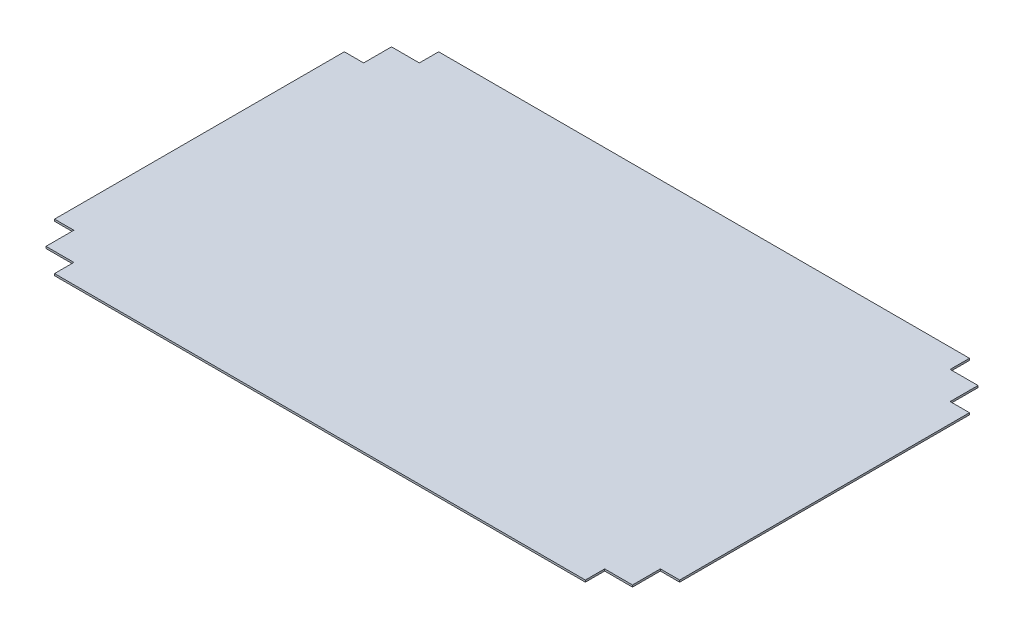
SolidWorks part; units mm, degrees
ref_plane "Front Plane" through (0, 0, 0) normal (0, 0, 1) x (1, 0, 0)
ref_plane "Top Plane" through (0, 0, 0) normal (0, 1, 0) x (1, 0, 0)
ref_plane "Right Plane" through (0, 0, 0) normal (1, 0, 0) x (0, 0, -1)
sketch "Sketch1" plane through (0, 0, 0) normal (0, 1, 0) x (1, 0, 0)
  line L0 (-325.4993, 150.9011) -> (-307.0007, 150.9011)
  line L1 (-307.0007, 150.9011) -> (-305.4007, 150.9011)
  line L2 (-305.4007, 150.9011) -> (-305.4007, 179.9011)
  line L3 (-305.4007, 179.9011) -> (-276.4007, 179.9011)
  line L4 (-276.4007, 179.9011) -> (-276.4007, 199.9989)
  line L5 (-276.4007, 199.9989) -> (276.4007, 199.9989)
  line L6 (276.4007, 199.9989) -> (276.4007, 179.9011)
  line L7 (276.4007, 179.9011) -> (305.4007, 179.9011)
  line L8 (305.4007, 179.9011) -> (305.4007, 150.9011)
  line L9 (305.4007, 150.9011) -> (325.4993, 150.9011)
  line L10 (325.4993, 150.9011) -> (325.4993, -150.9011)
  line L11 (325.4993, -150.9011) -> (305.4007, -150.9011)
  line L12 (305.4007, -150.9011) -> (305.4007, -179.9011)
  line L13 (305.4007, -179.9011) -> (276.4007, -179.9011)
  line L14 (276.4007, -179.9011) -> (276.4007, -199.9989)
  line L15 (276.4007, -199.9989) -> (-276.4007, -199.9989)
  line L16 (-276.4007, -199.9989) -> (-276.4007, -179.9011)
  line L17 (-276.4007, -179.9011) -> (-305.4007, -179.9011)
  line L18 (-305.4007, -179.9011) -> (-305.4007, -150.9011)
  line L19 (-305.4007, -150.9011) -> (-325.4993, -150.9011)
  line L20 (-325.4993, -150.9011) -> (-325.4993, 150.9011)
extrude "Boss-Extrude1" add sketch "Sketch1" along normal blind 2
